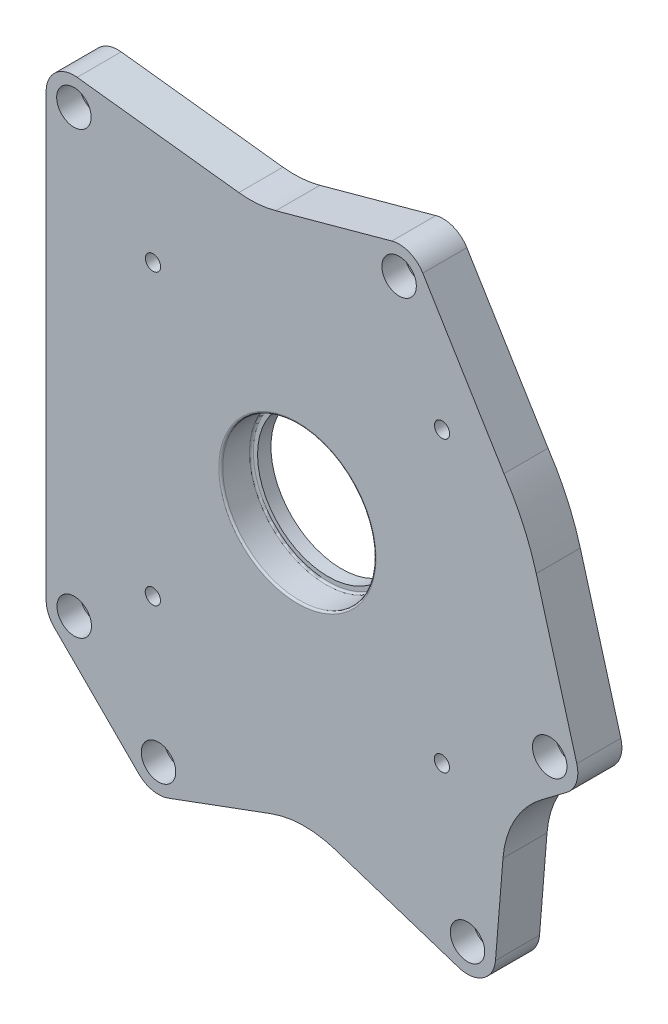
SolidWorks part; units mm, degrees
material "6061-T6 (SS)"
ref_plane "Front Plane" through (0, 0, 0) normal (0, 0, 1) x (1, 0, 0)
ref_plane "Top Plane" through (0, 0, 0) normal (0, 1, 0) x (1, 0, 0)
ref_plane "Right Plane" through (0, 0, 0) normal (1, 0, 0) x (0, 0, -1)
sketch "Sketch1" plane through (0, 0, 0) normal (0, 0, 1) x (1, 0, 0)
  line L0 (84.2211, -163.4901) -> (2.6993, -136.8316)
  line L1 (-67.4584, -162.7302) -> (2.6993, -136.8316)
  line L2 (-82.9108, -159.3414) -> (-126.9141, -115.3364)
  line L3 (140.5448, -56.1387) -> (109.1493, -79.774)
  line L4 (103.4012, -150.7323) -> (109.1493, -79.774)
  line L5 (145.8454, -40.4558) -> (124.6838, 34.9416)
  line L6 (65.4504, 141.1198) -> (107.841, 71.6428)
  line L9 (49.2431, 147.5528) -> (-20.7968, 128.3749)
  line L13 (-115.0226, 139.4368) -> (-20.7968, 128.3749)
  line L14 (-131.2133, 125.0355) -> (-131.2102, -104.9645)
  arc A2 (-115.0226, 139.4368) -> (-131.2133, 125.0355) centre (-116.7133, 125.0357) ccw
  circle A3 centre (-116.7133, 125.0357) radius 3.5 construction
  arc A6 (65.4504, 141.1198) -> (49.2431, 147.5528) centre (53.0725, 133.5676) ccw
  circle A7 centre (-76.5534, 103.7539) radius 2.5 construction
  arc A9 (-131.2102, -104.9645) -> (-126.9141, -115.3364) centre (-116.5415, -104.9643) ccw
  circle A10 centre (-116.5415, -104.9643) radius 3.5 construction
  arc A12 (-82.9108, -159.3414) -> (-67.4584, -162.7302) centre (-72.5383, -148.9692) ccw
  circle A13 centre (-72.5383, -148.9692) radius 3.5 construction
  arc A15 (84.2211, -163.4901) -> (103.4012, -150.7323) centre (88.7803, -149.548) ccw
  arc A17 (140.5448, -56.1387) -> (145.8454, -40.4558) centre (131.7224, -44.4197) ccw
  circle A18 centre (59.1026, -114.9804) radius 2.5 construction
  circle A23 centre (88.7803, -149.548) radius 3.5 construction
  circle A27 centre (131.7224, -44.4197) radius 3.5 construction
  arc A30 (124.6838, 34.9416) -> (107.841, 71.6428) centre (-0.017, -0.0702) ccw
  circle A31 centre (53.0725, 133.5676) radius 3.5 construction
  dimension "D1" = 14.5
  dimension "D2" = 7
  dimension "D3" = 5
extrude "Boss-Extrude1" add sketch "Sketch1" along normal blind 23 contours L5 A30 L6 A6 L9 L13 A2 L14 A9 L2 A12 L1 L0 A15 L4 L3 A17 A31 A3 A7 A10 A13 A18 A23 A27
fillet "Fillet2" radius 50.8 3 edges at (-20.7968, 128.3749, 11.5) (109.1493, -79.774, 11.5) (2.6993, -136.8316, 11.5)
sketch "Sketch2" plane through (0, 0, 23) normal (0, 0, -1) x (-1, 0, 0)
  circle A0 centre (0, 0) radius 40.05
  dimension "D1" = 80.1
extrude "Cut-Extrude1" cut sketch "Sketch2" along normal blind 16
sketch "Sketch5" plane through (0, 0, 23) normal (0, 0, -1) x (-1, 0, 0)
  circle A0 centre (0, 0) radius 36.83
  dimension "D1" = 73.66
extrude "Cut-Extrude2" cut sketch "Sketch5" along normal blind 25.4
sketch "Sketch6" [suppressed] plane through (0, 0, 0) normal (0, 0, 1) x (1, 0, 0)
  circle A0 centre (0, 0) radius 50.8 construction
  point P14 (0, 0)
  dimension "D2" = 101.6
fillet "Fillet5" radius 1 1 edges at (-40.05, 0, 23)
fillet "Fillet6" radius 1 1 edges at (-40.05, 0, 7)
sketch "Sketch43" [suppressed] plane through (0, 0, 23) normal (0, 0, 1) x (1, 0, 0)
  line L13 (0, 0) -> (150.4649, 0) construction
  line L14 (-31.12, -98.35) -> (-105.6166, -112.2929) construction
  line L15 (-31, 98) -> (-105.6166, 111.6261) construction
  line L16 (-105.6166, -112.2929) -> (-105.6166, 111.6261) construction
  line L17 (0, 0) -> (-105.6166, 111.6261) construction
  line L18 (-31, 98) -> (0, 0) construction
  line L19 (0, 0) -> (46, 97.92) construction
  line L20 (77.9, 39.75) -> (0, 0) construction
  line L21 (0, 0) -> (-72, -98.1221) construction
  line L22 (0, 0) -> (78.925, -30.46) construction
  line L23 (45.85, -98.52) -> (0, 0) construction
  line L24 (0, 0) -> (-72, 97.9779) construction
  line L25 (0, 0) -> (-31.12, -98.35) construction
  line L26 (-105.6166, -112.2929) -> (0, 0) construction
  circle A8 centre (0, 0) radius 46.4211 construction
  circle A12 centre (-46.643, -71.23) radius 11.3319 construction
  circle A13 centre (-72, 97.9779) radius 3.9701
  circle A14 centre (-72, -98.1221) radius 3.9701
  circle A15 centre (-105.6166, 111.6261) radius 3
  circle A16 centre (-31, 98) radius 3
  circle A17 centre (46, 97.92) radius 3
  circle A18 centre (77.9, 39.75) radius 3
  circle A19 centre (78.925, -30.46) radius 3
  circle A20 centre (45.85, -98.52) radius 3
  circle A21 centre (-31.12, -98.35) radius 3
  circle A22 centre (-105.6166, -112.2929) radius 3
  circle A23 centre (0, 0) radius 36.83 construction
  dimension "D2" = 45.85
  dimension "D3" = 31.12
  dimension "D1" = 98.52
  dimension "D4" = 98.35
  dimension "D5" = 98.1221
  dimension "D6" = 72
  dimension "D7" = 105.6166
  dimension "D8" = 105.6166
  dimension "D9" = 72
  dimension "D10" = 31
  dimension "D11" = 46
  dimension "D12" = 77.9
  dimension "D13" = 78.925
  dimension "D14" = 39.75
  dimension "D15" = 30.46
  dimension "D16" = 97.92
  dimension "D17" = 98
  dimension "D18" = 97.9779
  dimension "D19" = 111.6261
  dimension "D20" = 112.2929
  dimension "D21" = 196.1
  dimension "D22" = 7.9403
  dimension "D23" = 6
sketch "Sketch59" plane through (0, 0, 23) normal (0, 0, 1) x (1, 0, 0)
  line L0 (145.8454, -40.4558) -> (124.6838, 34.9416) construction
  line L1 (140.5448, -56.1387) -> (127.387, -66.0442) construction
  line L2 (103.4012, -150.7323) -> (107.3061, -102.5275) construction
  line L3 (84.2211, -163.4901) -> (19.4993, -142.3254) construction
  line L4 (-67.4584, -162.7302) -> (-13.8824, -142.9527) construction
  line L5 (-82.9108, -159.3414) -> (-126.9141, -115.3364) construction
  line L6 (65.4504, 141.1198) -> (107.841, 71.6428) construction
  line L7 (49.2431, 147.5528) -> (-11.269, 130.9837) construction
  line L8 (-115.0226, 139.4368) -> (-30.608, 129.5267) construction
  line L9 (-131.2133, 125.0355) -> (-131.2102, -104.9645) construction
  line L10 (145.8454, -40.4558) -> (124.6838, 34.9416)
  line L11 (140.5448, -56.1387) -> (127.387, -66.0442)
  line L12 (103.4012, -150.7323) -> (107.3061, -102.5275)
  line L13 (84.2211, -163.4901) -> (19.4993, -142.3254)
  line L14 (-67.4584, -162.7302) -> (-13.8824, -142.9527)
  line L15 (-82.9108, -159.3414) -> (-126.9141, -115.3364)
  line L16 (65.4504, 141.1198) -> (107.841, 71.6428)
  line L17 (49.2431, 147.5528) -> (-11.269, 130.9837)
  line L18 (-115.0226, 139.4368) -> (-30.608, 129.5267)
  line L19 (-131.2133, 125.0355) -> (-131.2102, -104.9645)
  line L30 (49.2431, 147.5528) -> (-20.7968, 128.3749)
  line L31 (107.841, 71.6428) -> (65.4504, 141.1198)
  line L32 (145.8454, -40.4558) -> (124.6838, 34.9416)
  line L33 (109.1493, -79.774) -> (140.5448, -56.1387)
  line L34 (103.4012, -150.7323) -> (109.1493, -79.774)
  line L35 (2.6993, -136.8316) -> (84.2211, -163.4901)
  line L36 (-67.4584, -162.7302) -> (2.6993, -136.8316)
  line L37 (-126.9141, -115.3364) -> (-82.9108, -159.3414)
  line L38 (-131.2133, 125.0355) -> (-131.2102, -104.9645)
  line L39 (-20.7968, 128.3749) -> (-115.0226, 139.4368)
  line L40 (49.2431, 147.5528) -> (-20.7968, 128.3749)
  line L41 (107.841, 71.6428) -> (65.4504, 141.1198)
  line L42 (145.8454, -40.4558) -> (124.6838, 34.9416)
  line L43 (109.1493, -79.774) -> (140.5448, -56.1387)
  line L44 (103.4012, -150.7323) -> (109.1493, -79.774)
  line L45 (2.6993, -136.8316) -> (84.2211, -163.4901)
  line L46 (-67.4584, -162.7302) -> (2.6993, -136.8316)
  line L47 (-126.9141, -115.3364) -> (-82.9108, -159.3414)
  line L48 (-131.2133, 125.0355) -> (-131.2102, -104.9645)
  line L49 (-20.7968, 128.3749) -> (-115.0226, 139.4368)
  arc A0 (124.6838, 34.9416) -> (107.841, 71.6428) centre (-0.017, -0.0702) ccw construction
  arc A1 (140.5448, -56.1387) -> (145.8454, -40.4558) centre (131.7224, -44.4197) ccw construction
  arc A2 (127.387, -66.0442) -> (107.3061, -102.5275) centre (157.9402, -106.6292) ccw construction
  arc A3 (84.2211, -163.4901) -> (103.4012, -150.7323) centre (88.7803, -149.548) ccw construction
  arc A4 (19.4993, -142.3254) -> (-13.8824, -142.9527) centre (3.7099, -190.6093) ccw construction
  arc A5 (-82.9108, -159.3414) -> (-67.4584, -162.7302) centre (-72.5383, -148.9692) ccw construction
  arc A6 (-131.2102, -104.9645) -> (-126.9141, -115.3364) centre (-116.5415, -104.9643) ccw construction
  arc A7 (65.4504, 141.1198) -> (49.2431, 147.5528) centre (53.0725, 133.5676) ccw construction
  arc A8 (-30.608, 129.5267) -> (-11.269, 130.9837) centre (-24.6849, 179.9802) ccw construction
  arc A9 (-115.0226, 139.4368) -> (-131.2133, 125.0355) centre (-116.7133, 125.0357) ccw construction
  arc A10 (124.6838, 34.9416) -> (107.841, 71.6428) centre (-0.017, -0.0702) ccw
  arc A11 (140.5448, -56.1387) -> (145.8454, -40.4558) centre (131.7224, -44.4197) ccw
  arc A12 (127.387, -66.0442) -> (107.3061, -102.5275) centre (157.9402, -106.6292) ccw
  arc A13 (84.2211, -163.4901) -> (103.4012, -150.7323) centre (88.7803, -149.548) ccw
  arc A14 (19.4993, -142.3254) -> (-13.8824, -142.9527) centre (3.7099, -190.6093) ccw
  arc A15 (-82.9108, -159.3414) -> (-67.4584, -162.7302) centre (-72.5383, -148.9692) ccw
  arc A16 (-131.2102, -104.9645) -> (-126.9141, -115.3364) centre (-116.5415, -104.9643) ccw
  arc A17 (65.4504, 141.1198) -> (49.2431, 147.5528) centre (53.0725, 133.5676) ccw
  arc A18 (-30.608, 129.5267) -> (-11.269, 130.9837) centre (-24.6849, 179.9802) ccw
  arc A19 (-115.0226, 139.4368) -> (-131.2133, 125.0355) centre (-116.7133, 125.0357) ccw
  circle A20 centre (-116.7133, 125.0357) radius 3.5 construction
  circle A21 centre (-76.5534, 103.7539) radius 2.5 construction
  circle A22 centre (-116.5415, -104.9643) radius 3.5 construction
  circle A23 centre (-72.5383, -148.9692) radius 3.5 construction
  circle A24 centre (59.1026, -114.9804) radius 2.5 construction
  circle A25 centre (88.7803, -149.548) radius 3.5 construction
  circle A26 centre (131.7224, -44.4197) radius 3.5 construction
  arc A27 (65.4504, 141.1198) -> (49.2431, 147.5528) centre (53.0725, 133.5676) ccw
  arc A28 (124.6838, 34.9416) -> (107.841, 71.6428) centre (-0.017, -0.0702) ccw
  arc A29 (140.5448, -56.1387) -> (145.8454, -40.4558) centre (131.7224, -44.4197) ccw
  arc A30 (84.2211, -163.4901) -> (103.4012, -150.7323) centre (88.7803, -149.548) ccw
  arc A31 (-82.9108, -159.3414) -> (-67.4584, -162.7302) centre (-72.5383, -148.9692) ccw
  arc A32 (-131.2102, -104.9645) -> (-126.9141, -115.3364) centre (-116.5415, -104.9643) ccw
  arc A33 (-115.0226, 139.4368) -> (-131.2133, 125.0355) centre (-116.7133, 125.0357) ccw
  arc A34 (65.4504, 141.1198) -> (49.2431, 147.5528) centre (53.0725, 133.5676) ccw
  arc A35 (124.6838, 34.9416) -> (107.841, 71.6428) centre (-0.017, -0.0702) ccw
  arc A36 (140.5448, -56.1387) -> (145.8454, -40.4558) centre (131.7224, -44.4197) ccw
  arc A37 (84.2211, -163.4901) -> (103.4012, -150.7323) centre (88.7803, -149.548) ccw
  arc A38 (-82.9108, -159.3414) -> (-67.4584, -162.7302) centre (-72.5383, -148.9692) ccw
  arc A39 (-131.2102, -104.9645) -> (-126.9141, -115.3364) centre (-116.5415, -104.9643) ccw
  arc A40 (-115.0226, 139.4368) -> (-131.2133, 125.0355) centre (-116.7133, 125.0357) ccw
  circle A41 centre (53.0725, 133.5676) radius 3.5 construction
  dimension "D1" = 0
hole_wizard "CBORE for M10 SHCS7" positions "Sketch62" profile "Sketch63" counterbore size "M10" standard "ANSI Metric" end condition through all
sketch "Sketch62" plane through (0, 0, 23) normal (0, 0, 1) x (1, 0, 0)
  point P0 (-116.7133, 125.0357)
  point P3 (-116.5415, -104.9643)
  point P7 (-72.5383, -148.9692)
  point P10 (53.0725, 133.5676)
  point P13 (131.7224, -44.4197)
  point P16 (88.7803, -149.548)
sketch "Sketch63" plane through (-116.7133, 125.0357, 23) normal (1, 0, 0) x (0, -1, 0)
  line L0 (0, 0) -> (0, 23)
  line L1 (0, 23) -> (5.25, 23)
  line L3 (5.25, 23) -> (5.25, 12)
  line L4 (5.25, 12) -> (9, 12)
  line L5 (9, 12) -> (9, 0)
  line L7 (9, 0) -> (0, 0)
  line L11 (0, -6.35) -> (0, 107.95) construction
  dimension "Thru Hole Dia." = 10.5
  dimension "Thru Hole Depth" = 23
  dimension "C'Bore Dia." = 18
  dimension "C'Bore Depth" = 12
hole_wizard "Tap Drill for M8x1.25 Tap2" [suppressed] positions "Sketch66" profile "Sketch67" hole size "M8x1.25" standard "ANSI Metric"
sketch "Sketch66" [suppressed] plane through (0, 0, 23) normal (0, 0, 1) x (1, 0, 0)
  point P0 (46, 97.92)
  point P3 (-31, 98)
  point P6 (-105.6166, 111.6261)
  point P9 (-105.6166, -112.2929)
  point P12 (-31.12, -98.35)
  point P15 (45.85, -98.52)
  point P18 (78.925, -30.46)
  point P21 (77.9, 39.75)
sketch "Sketch67" plane through (46, 97.92, 23) normal (1, 0, 0) x (0, -1, 0)
  line L0 (0, 0) -> (0, 23)
  line L1 (0, 23) -> (3.4, 23)
  line L2 (3.4, 23) -> (3.4, 0)
  line L5 (3.4, 0) -> (0, 0)
  line L11 (0, -6.35) -> (0, 107.95) construction
  dimension "Thru Hole Dia." = 6.8
  dimension "Thru Hole Depth" = 23
hole_wizard "Ø8.0mm Dowel Hole1" [suppressed] positions "Sketch70" profile "Sketch71" hole size "Ø8.0" standard "ANSI Metric"
sketch "Sketch70" [suppressed] plane through (0, 0, 23) normal (0, 0, 1) x (1, 0, 0)
  point P0 (-72, 97.9779)
  point P3 (-72, -98.1221)
sketch "Sketch71" plane through (-72, 97.9779, 23) normal (1, 0, 0) x (0, -1, 0)
  line L0 (0, 0) -> (0, 11.4034)
  line L1 (0, 11.4034) -> (4, 9)
  line L2 (4, 9) -> (4, 0)
  line L5 (4, 0) -> (0, 0)
  line L10 (0, 11.4034) -> (-4, 9) construction
  line L11 (0, -6.35) -> (0, 107.95) construction
  dimension "Hole Dia." = 8
  dimension "Hole Depth" = 9
  dimension "Drill Angle" = 118
hole_wizard "Ø10.0mm Dowel Hole3" positions "Sketch72" profile "Sketch73" hole size "Ø10.0" standard "ANSI Metric"
sketch "Sketch72" plane through (0, 0, 0) normal (0, 0, -1) x (-1, 0, 0)
  point P0 (76.5534, 103.7539)
  point P3 (-59.1026, -114.9804)
sketch "Sketch73" plane through (-76.5534, 103.7539, 0) normal (1, 0, 0) x (0, 1, 0)
  line L0 (0, 0) -> (0, 13.0043)
  line L1 (0, 13.0043) -> (5, 10)
  line L2 (5, 10) -> (5, 0)
  line L5 (5, 0) -> (0, 0)
  line L10 (0, 13.0043) -> (-5, 10) construction
  line L11 (0, -6.35) -> (0, 107.95) construction
  dimension "Hole Dia." = 10
  dimension "Hole Depth" = 10
  dimension "Drill Angle" = 118
hole_wizard "CBORE for M10 SHCS9" [suppressed] positions "Sketch74" profile "Sketch75" counterbore size "M10" standard "ANSI Metric"
sketch "Sketch74" plane through (0, 0, 23) normal (0, 0, 1) x (1, 0, 0)
  point P0 (53.0725, 133.5676)
  point P3 (131.7224, -44.4197)
  point P6 (88.7803, -149.548)
  point P9 (-116.7133, 125.0357)
  point P12 (-116.5415, -104.9643)
  point P15 (-72.5383, -148.9692)
  point P18 (-116.7133, 125.0357)
  point P21 (-116.5415, -104.9643)
  point P24 (-72.5383, -148.9692)
sketch "Sketch75" plane through (53.0725, 133.5676, 23) normal (1, 0, 0) x (0, -1, 0)
  line L0 (0, 0) -> (0, 23)
  line L1 (0, 23) -> (5.25, 23)
  line L3 (5.25, 23) -> (5.25, 10)
  line L4 (5.25, 10) -> (9, 10)
  line L5 (9, 10) -> (9, 0)
  line L7 (9, 0) -> (0, 0)
  line L11 (0, -6.35) -> (0, 107.95) construction
  dimension "Thru Hole Dia." = 10.5
  dimension "Thru Hole Depth" = 23
  dimension "C'Bore Dia." = 18
  dimension "C'Bore Depth" = 10
sketch "Sketch76" plane through (0, 0, 23) normal (0, 0, 1) x (1, 0, 0)
  line L0 (-0.017, -0.0702) -> (106.663, -0.0702) construction
  line L1 (-0.017, -0.0702) -> (-0.017, -106.7502) construction
  line L2 (-0.017, -0.0702) -> (75.4171, -75.5044) construction
  circle A0 centre (-0.017, -0.0702) radius 106.68 construction
  circle A6 centre (75.4171, -75.5044) radius 5
  circle A7 centre (-75.5044, -75.4171) radius 5
  circle A8 centre (-75.4171, 75.5044) radius 5
  circle A9 centre (75.5044, 75.4171) radius 5
  point P15 (-0.017, -0.0702)
  point P19 (0, 0)
  dimension "D1" = 213.36
  dimension "D4" = 10
  dimension "D3" = 45
  dimension "D2" = 4
hole_wizard "Tap Drill for 3/8-16 Tap1" positions "3DSketch1" profile "Sketch77" hole size "3/8-16" standard "ANSI Inch" end condition through all
sketch3d "3DSketch1"
  point P0 (75.5044, 75.4171, 23)
  point P3 (-75.4171, 75.5044, 23)
  point P6 (-75.5044, -75.4171, 23)
  point P9 (75.4171, -75.5044, 23)
sketch "Sketch77" plane through (75.5044, 75.4171, 23) normal (1, 0, 0) x (0, -1, 0)
  line L0 (0, 0) -> (0, 23)
  line L1 (0, 23) -> (3.9687, 23)
  line L2 (3.9687, 23) -> (3.9687, 0)
  line L5 (3.9687, 0) -> (0, 0)
  line L11 (0, -6.35) -> (0, 107.95) construction
  dimension "Thru Hole Dia." = 7.9375
  dimension "Thru Hole Depth" = 23
equation "\"117.300x2\"=117.3"
